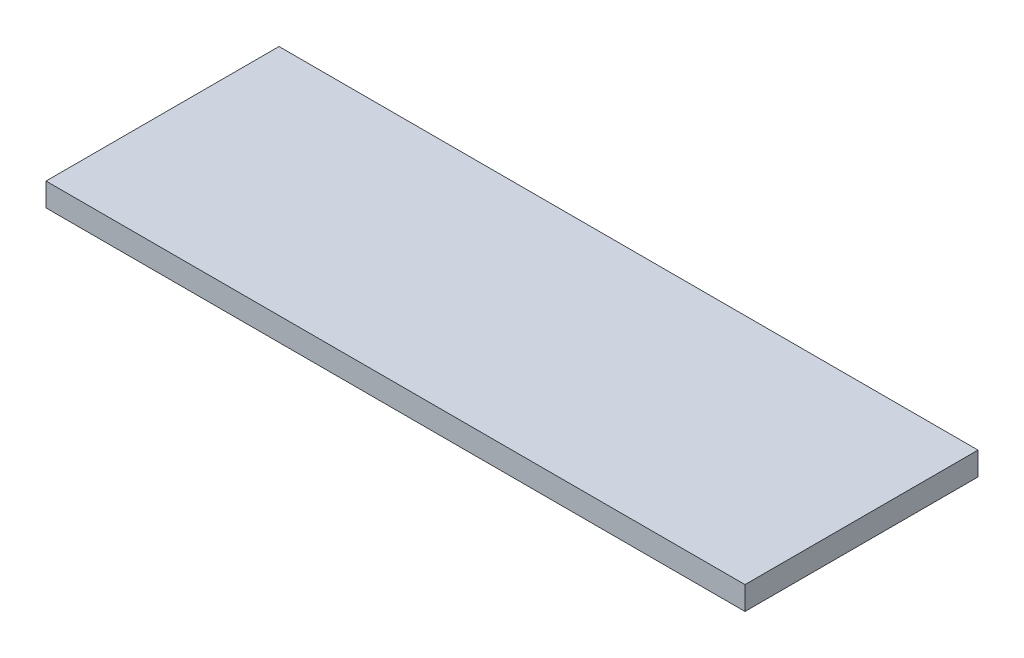
SolidWorks part; units mm, degrees
ref_plane "Front Plane" through (0, 0, 0) normal (0, 0, 1) x (1, 0, 0)
ref_plane "Top Plane" through (0, 0, 0) normal (0, 1, 0) x (1, 0, 0)
ref_plane "Right Plane" through (0, 0, 0) normal (1, 0, 0) x (0, 0, -1)
sketch "Sketch1" plane through (0, 0, 0) normal (0, 1, 0) x (1, 0, 0)
  line L1 (0, 0) -> (30, 0)
  line L2 (0, 0) -> (0, 10)
  line L3 (0, 10) -> (30, 10)
  line L4 (30, 0) -> (30, 10)
  dimension "D1" = 10
  dimension "D2" = 30
extrude "Boss-Extrude1" add sketch "Sketch1" along normal blind 1
